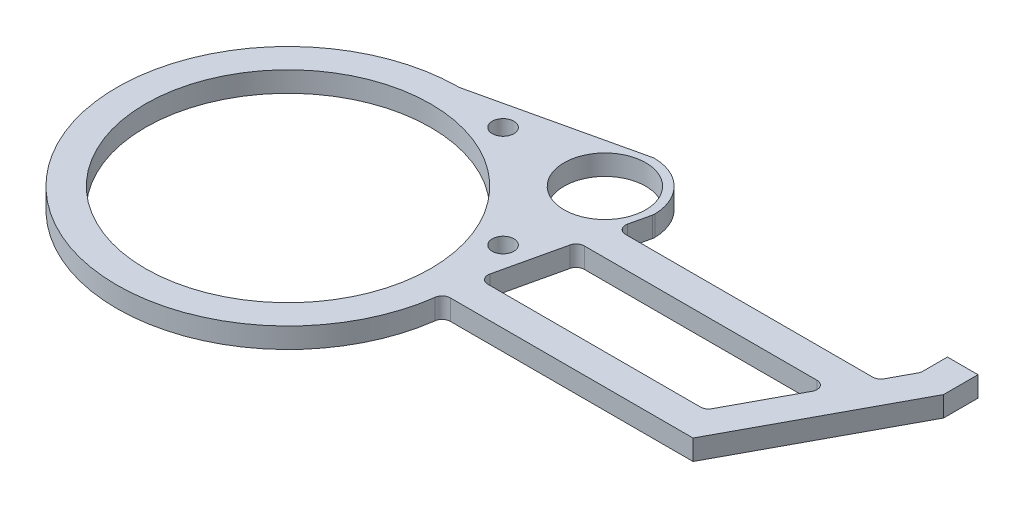
SolidWorks part; units mm, degrees
material "6061-T6 (SS)"
ref_plane "Front Plane" through (0, 0, 0) normal (0, 0, 1) x (1, 0, 0)
ref_plane "Top Plane" through (0, 0, 0) normal (0, 1, 0) x (1, 0, 0)
ref_plane "Right Plane" through (0, 0, 0) normal (1, 0, 0) x (0, 0, -1)
sketch "Sketch1" plane through (0, 0, 0) normal (0, 1, 0) x (1, 0, 0)
  line L0 (0, 0) -> (49.3914, 49.3914) construction
  line L1 (0, 53.3781) -> (49.3914, 64.6695)
  line L2 (53.3781, 0) -> (64.6695, 49.3914)
  circle A2 centre (0, 0) radius 53.3781 construction
  circle A3 centre (49.3914, 49.3914) radius 15.2781 construction
  arc A4 (49.3914, 64.6695) -> (64.6695, 49.3914) centre (49.3914, 49.3914) cw
  arc A5 (0, 53.3781) -> (53.3781, 0) centre (0, 0) ccw
  dimension "D1" = 53.3781
extrude "Boss-Extrude1" add sketch "Sketch1" along normal blind 6.35
fillet "Fillet2" radius 6.35 2 edges at (53.3781, 3.175, 0) (0, 3.175, -53.3781)
sketch "Sketch4" plane through (0, 6.35, 0) normal (0, 1, 0) x (1, 0, 0)
  line L0 (52.07, -0.0823) -> (128.27, -0.0823) construction
  line L1 (52.07, -4.8448) -> (131.1165, -4.8448)
  line L2 (128.27, -0.0823) -> (153.67, 47.1544) construction
  line L3 (153.67, 47.1544) -> (153.67, 56.6794) construction
  line L4 (131.1165, -4.8448) -> (158.4325, 45.9552)
  line L5 (158.4325, 45.9552) -> (158.4325, 56.6794)
  line L6 (52.07, 4.6802) -> (125.4235, 4.6802)
  line L7 (125.4235, 4.6802) -> (139.0815, 30.0802)
  line L8 (148.9075, 48.3537) -> (148.9075, 56.6794)
  line L9 (52.07, -4.8448) -> (52.07, 4.6802)
  line L10 (158.4325, 56.6794) -> (148.9075, 56.6794)
  line L11 (52.07, -0.0823) -> (128.27, -0.0823) construction
  line L12 (144.2033, 39.6052) -> (148.9075, 48.3537)
  line L13 (52.07, 39.6052) -> (144.2033, 39.6052)
  line L14 (52.07, 39.6052) -> (52.07, 30.0802)
  line L15 (52.07, 30.0802) -> (139.0815, 30.0802)
  line L18 (125.4235, 4.6802) -> (148.9075, 48.3537) construction
  dimension "D1" = 52.07
  dimension "D4" = 76.2
  dimension "D5" = 9.525
  dimension "D6" = 101.6
  dimension "D7" = 50.8
  dimension "D8" = 25.4
  dimension "D9" = 9.525
  dimension "D2" = 4.7625
  dimension "D3" = 4.7625
extrude "Boss-Extrude2" add sketch "Sketch4" against normal blind 6.35
sketch "Sketch3" plane through (0, 6.35, 0) normal (0, 1, 0) x (1, 0, 0)
  line L0 (0, 0) -> (49.3914, 49.3914) construction
  circle A0 centre (0, 0) radius 44.4754
  circle A1 centre (49.3914, 49.3914) radius 12.7254
  dimension "D1" = 88.9508
  dimension "D2" = 25.4508
extrude "Cut-Extrude1" cut sketch "Sketch3" against normal through all
fillet "Fillet3" radius 2.54 10 edges at (54.448, 3.175, -4.6802) (53.1578, 3.175, 4.8448) (49.3914, 3.175, -64.6695) (64.6695, 3.175, -49.3914) (60.2548, 3.175, -30.0802) (148.9075, 3.175, -48.3537) (139.0815, 3.175, -30.0802) (125.4235, 3.175, -4.6802) (144.2033, 3.175, -39.6052) (62.4323, 3.175, -39.6052)
hole_wizard "#6-32 Tapped Hole1" positions "Sketch6" profile "Sketch5" tap size "#6-32" standard "Ansi Inch"
sketch "Sketch6" plane through (0, 0, -56.6794) normal (0, 0, -1) x (-1, 0, 0)
  line L0 (-153.67, 0) -> (-153.67, 6.35) construction
  line L1 (-158.4325, 0) -> (-148.9075, 0) construction
  line L2 (-158.4325, 6.35) -> (-148.9075, 6.35) construction
  point P0 (-153.67, 3.175)
sketch "Sketch5" plane through (153.67, 3.175, -56.6794) normal (1, 0, 0) x (0, 1, 0)
  line L0 (0, 0) -> (0, 10.2107)
  line L1 (0, 10.2107) -> (1.3525, 9.398)
  line L2 (1.3525, 9.398) -> (1.3525, 7.112)
  line L3 (1.3525, 7.112) -> (1.7526, 7.112)
  line L4 (1.7526, 7.112) -> (1.7526, 0)
  line L5 (1.7526, 0) -> (0, 0)
  line L10 (0, 10.2107) -> (-1.3526, 9.398) construction
  line L11 (0, -6.35) -> (0, 107.95) construction
  dimension "Tap Drill Dia." = 2.7051
  dimension "Tap Drill Depth" = 9.398
  dimension "Thread Major Dia." = 3.5052
  dimension "Thread Depth" = 7.112
  dimension "Drill Angle" = 118
sketch "Sketch7" plane through (0, 0, -56.6794) normal (0, 0, -1) x (-1, 0, 0)
  line L0 (-158.4325, 3.175) -> (-148.9075, 3.175) construction
  line L1 (-158.4325, 0) -> (-158.4325, 6.35) construction
  line L2 (-148.9075, 0) -> (-148.9075, 6.35) construction
sketch "Sketch8" [suppressed] plane through (0, 0, 0) normal (0, -1, 0) x (1, 0, 0)
  line L0 (0, 0) -> (49.3914, -49.3914) construction
  circle A0 centre (0, 0) radius 50.8381
  circle A1 centre (49.3914, -49.3914) radius 12.7381
  dimension "D1" = 101.6762
  dimension "D2" = 25.4762
extrude "Cut-Extrude2" [suppressed] cut sketch "Sketch8" against normal blind 3.175
hole_wizard "1/4 Clearance Hole1" positions "Sketch10" profile "Sketch9" hole size "1/4" standard "Ansi Inch"
sketch "Sketch10" plane through (0, 0, 0) normal (0, -1, 0) x (1, 0, 0)
  line L2 (49.3914, -49.3914) -> (49.3914, -17.6414) construction
  line L4 (49.3914, -49.3914) -> (17.6414, -49.3914) construction
  point P0 (49.3914, -17.6414)
  point P16 (17.6414, -49.3914)
  dimension "D1" = 31.75
  dimension "D2" = 31.75
sketch "Sketch9" plane through (49.3914, 0, -17.6414) normal (1, 0, 0) x (0, 0, -1)
  line L0 (0, 0) -> (0, 27.4298)
  line L1 (0, 27.4298) -> (3.3782, 25.4)
  line L2 (3.3782, 25.4) -> (3.3782, 0)
  line L5 (3.3782, 0) -> (0, 0)
  line L10 (0, 27.4298) -> (-3.3782, 25.4) construction
  line L11 (0, -6.35) -> (0, 107.95) construction
  dimension "Hole Dia." = 6.7564
  dimension "Hole Depth" = 25.4
  dimension "Drill Angle" = 118
sketch "Sketch11" [suppressed] plane through (0, 6.35, 0) normal (0, 1, 0) x (-1, 0, 0)
  circle A0 centre (0, 0) radius 44.4881
extrude "Boss-Extrude3" [suppressed] add sketch "Sketch11" against normal blind 2.54
